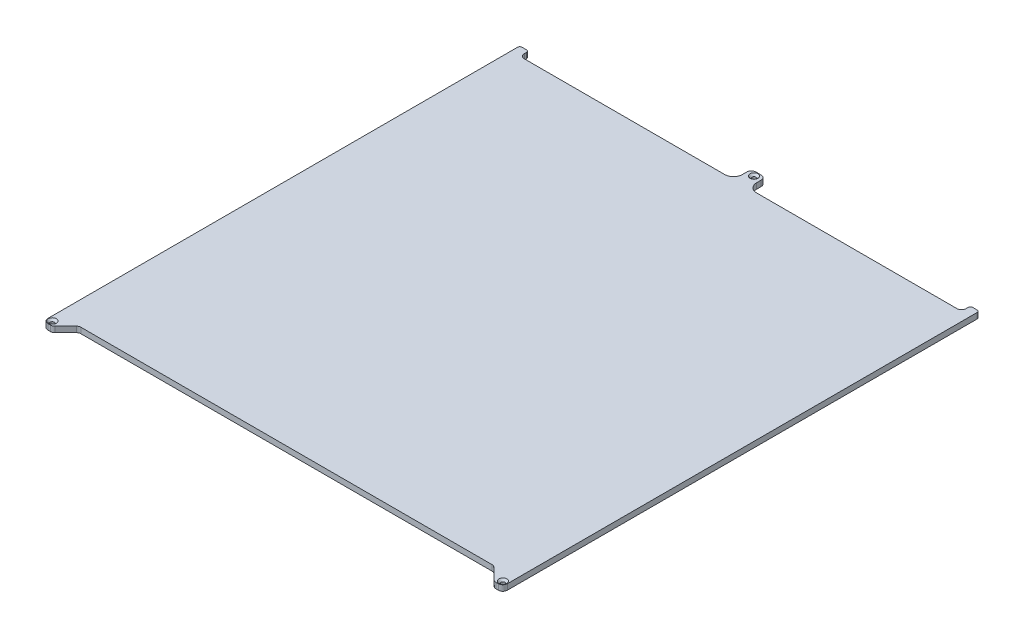
SolidWorks part; units mm, degrees
ref_plane "Front Plane" through (0, 0, 0) normal (0, 0, 1) x (1, 0, 0)
ref_plane "Top Plane" through (0, 0, 0) normal (0, 1, 0) x (1, 0, 0)
ref_plane "Right Plane" through (0, 0, 0) normal (1, 0, 0) x (0, 0, -1)
sketch "Sketch1" plane through (0, 0, 0) normal (0, 1, 0) x (1, 0, 0)
  line L0 (0, -1000) -> (0, 49000) construction
  line L1 (230.9289, -255) -> (-230.9289, -255)
  line L2 (-248, 260) -> (-248, 262.5)
  line L3 (-243, 255) -> (-18, 255)
  line L4 (258, -265) -> (258, 262.5)
  line L5 (-255.5, 265) -> (-250.5, 265)
  line L6 (-253, -270) -> (-250.0711, -270)
  line L7 (246.5355, -268.5355) -> (234.4645, -256.4645)
  line L8 (-246.5355, -268.5355) -> (-234.4645, -256.4645)
  line L9 (-258, -265) -> (-258, 262.5)
  line L10 (253, -270) -> (250.0711, -270)
  line L11 (18, 255) -> (243, 255)
  line L13 (255.5, 265) -> (250.5, 265)
  line L14 (248, 260) -> (248, 262.5)
  line L15 (-8, 265) -> (-8, 270)
  line L16 (-3, 275) -> (3, 275)
  line L17 (8, 265) -> (8, 270)
  arc A0 (250.5, 265) -> (248, 262.5) centre (250.5, 262.5) ccw
  arc A1 (258, 262.5) -> (255.5, 265) centre (255.5, 262.5) ccw
  circle A2 centre (0, 270) radius 5 construction
  arc A3 (243, 255) -> (248, 260) centre (243, 260) ccw
  arc A4 (234.4645, -256.4645) -> (230.9289, -255) centre (230.9289, -260) ccw
  arc A5 (250.0711, -270) -> (246.5355, -268.5355) centre (250.0711, -265) cw
  arc A6 (258, -265) -> (253, -270) centre (253, -265) cw
  arc A7 (-258, -265) -> (-253, -270) centre (-253, -265) ccw
  arc A8 (-250.0711, -270) -> (-246.5355, -268.5355) centre (-250.0711, -265) ccw
  arc A9 (-234.4645, -256.4645) -> (-230.9289, -255) centre (-230.9289, -260) cw
  arc A10 (-243, 255) -> (-248, 260) centre (-243, 260) cw
  arc A11 (-258, 262.5) -> (-255.5, 265) centre (-255.5, 262.5) cw
  arc A12 (-250.5, 265) -> (-248, 262.5) centre (-250.5, 262.5) cw
  arc A13 (-8, 265) -> (-18, 255) centre (-18, 265) cw
  arc A14 (8, 265) -> (18, 255) centre (18, 265) ccw
  arc A15 (3, 275) -> (8, 270) centre (3, 270) cw
  arc A16 (-8, 270) -> (-3, 275) centre (-3, 270) cw
  point P0 (0, 0)
  point P1 (0, -255)
  point P3 (-258, -270)
  point P14 (248, 265)
  point P17 (258, 265)
  point P26 (248, -270)
  point P29 (258, -270)
  point P48 (0, 255)
  point P49 (-248, -270)
  point P50 (-258, 265)
  point P51 (-248, 265)
  point P52 (0, 255)
  point P61 (8, 255)
  point P66 (251.5355, -270)
  dimension "D3" = 535
  dimension "D9" = 5
  dimension "D11" = 15
  dimension "D5" = 2.5
  dimension "D7" = 5
  dimension "D8" = 10
  dimension "D2" = 510
  dimension "D4" = 10
  dimension "D6" = 10
  dimension "D10" = 8
  dimension "D12" = 16
  dimension "D13" = 15
extrude "Boss-Extrude1" add sketch "Sketch1" along normal blind 6.35
hole_wizard "CSK for M4 SFHCS1" positions "Sketch2" profile "Sketch3" countersink size "M4" standard "ANSI Metric" end condition through all
sketch "Sketch2" plane through (0, 6.35, 0) normal (0, 1, 0) x (1, 0, 0)
  point P0 (0, 270)
  point P3 (253, -265)
  point P6 (-253, -265)
sketch "Sketch3" plane through (0, 6.35, -270) normal (1, 0, 0) x (0, 0, 1)
  line L0 (0, 0) -> (0, 6.35)
  line L1 (0, 6.35) -> (2.25, 6.35)
  line L2 (2.25, 6.35) -> (2.25, 2.23)
  line L3 (2.25, 2.23) -> (4.48, 0)
  line L5 (4.48, 0) -> (0, 0)
  line L6 (-2.25, 2.23) -> (-4.48, 0) construction
  line L11 (0, -6.35) -> (0, 107.95) construction
  dimension "Thru Hole Dia." = 4.5
  dimension "Thru Hole Depth" = 6.35
  dimension "Near C'Sink Dia." = 8.96
  dimension "Near C'Sink Angle" = 90
